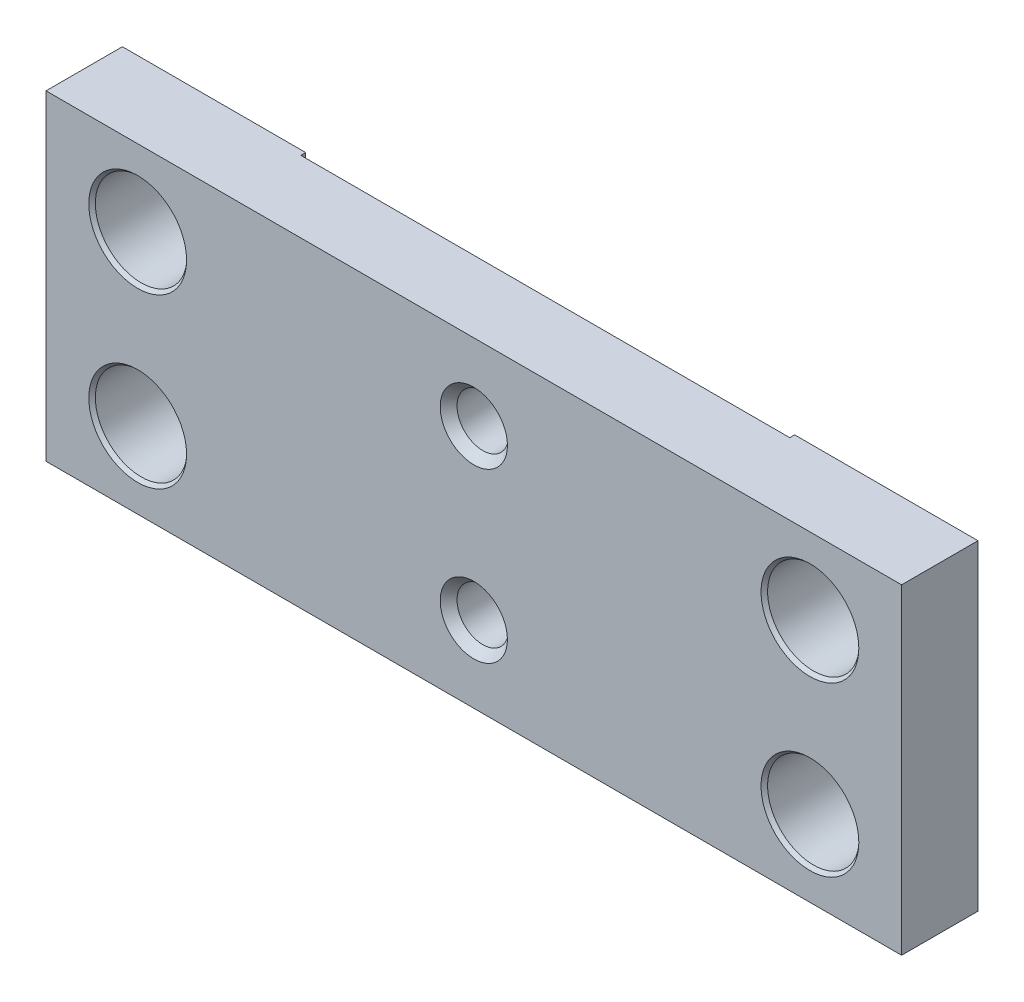
SolidWorks part; units mm, degrees
material "AISI 1018 Steel, Cold Rolled"
ref_plane "Front" through (0, 0, 0) normal (0, 0, 1) x (1, 0, 0)
ref_plane "Top" through (0, 0, 0) normal (0, 1, 0) x (1, 0, 0)
ref_plane "Right" through (0, 0, 0) normal (1, 0, 0) x (0, 0, -1)
sketch "Sketch1" plane through (0, 0, 0) normal (0, 0, 1) x (1, 0, 0)
  line L1 (-88.9, 0) -> (88.9, 0)
  line L2 (-88.9, 0) -> (-88.9, 66.675)
  line L3 (-88.9, 66.675) -> (88.9, 66.675)
  line L4 (88.9, 0) -> (88.9, 66.675)
  dimension "D1" = 66.675
  dimension "D2" = 177.8
extrude "Extrude1" add sketch "Sketch1" along normal blind 15.875
hole_wizard "1/2 Clearance Hole1" positions "Sketch12" profile "Sketch11" hole size "1/2" standard "Ansi Inch" end condition up to next
sketch "Sketch12" plane through (0, 0, 15.875) normal (0, 0, 1) x (1, 0, 0)
  line L0 (-69.85, 15.875) -> (69.85, 15.875) construction
  line L7 (-88.9, 33.3375) -> (88.9, 33.3375) construction
  line L8 (-88.9, 66.675) -> (-88.9, 0) construction
  line L9 (88.9, 0) -> (88.9, 66.675) construction
  line L12 (-69.85, 50.8) -> (69.85, 50.8) construction
  line L15 (0, 15.875) -> (0, 33.3375) construction
  line L16 (0, 33.3375) -> (0, 50.8) construction
  point P0 (-69.85, 50.8)
  point P1 (-69.85, 15.875)
  point P3 (69.85, 50.8)
  point P5 (69.85, 15.875)
  dimension "D1" = 34.925
  dimension "D3" = 139.7
sketch "Sketch11" plane through (-69.85, 50.8, 15.875) normal (1, 0, 0) x (0, -1, 0)
  line L0 (0, 0) -> (0, 15.875)
  line L1 (0, 15.875) -> (10.16, 15.875)
  line L2 (9.525, 15.1445) -> (9.525, 0.7305)
  line L3 (9.525, 0.7305) -> (10.16, 0)
  line L5 (10.16, 0) -> (0, 0)
  line L6 (-9.525, 0.7305) -> (-10.16, 0) construction
  line L7 (10.16, 15.875) -> (9.525, 15.1445)
  line L8 (-10.16, 15.875) -> (-9.525, 15.1445) construction
  line L11 (0, -6.35) -> (0, 107.95) construction
  dimension "Thru Hole Dia." = 19.05
  dimension "Thru Hole Depth" = 15.875
  dimension "Near C'Sink Dia." = 20.32
  dimension "Near C'Sink Angle" = 82
  dimension "Far C'Sink Dia." = 20.32
  dimension "Far C'Sink Angle" = 82
sketch "Sketch15" plane through (0, 0, 0) normal (0, 0, -1) x (-1, 0, 0)
  line L0 (-88.9, 66.675) -> (88.9, 66.675) construction
  line L1 (-50.8, 66.675) -> (50.8, 66.675)
  line L2 (-50.8, 66.675) -> (-50.8, 0)
  line L3 (-50.8, 0) -> (50.8, 0)
  line L4 (50.8, 66.675) -> (50.8, 0)
  line L5 (88.9, 0) -> (-88.9, 0) construction
  line L6 (88.9, 66.675) -> (88.9, 0) construction
  point P8 (0, 66.675)
  dimension "D1" = 38.1
extrude "Cut-Extrude1" cut sketch "Sketch15" against normal blind 1.016
sketch "Sketch17" plane through (0, 0, 0) normal (1, 0, 0) x (0, 0, -1)
  line L0 (-6.35, 0) -> (0, 10.9985)
  line L1 (-15.875, 0) -> (0, 0) construction
  line L2 (0, 0) -> (0, 66.675) construction
  line L3 (0, 10.9985) -> (0, 0)
  line L4 (0, 0) -> (-6.35, 0)
  line L5 (-15.875, 0) -> (-15.875, 66.675) construction
  dimension "D1" = 30
  dimension "D2" = 9.525
extrude "Cut-Extrude2" cut sketch "Sketch17" against normal mid plane 38.1
hole_wizard "1/2-13 Tapped Hole1" positions "Sketch14" profile "Sketch13" tap size "1/2-13" standard "Ansi Inch" end condition up to next
sketch "Sketch14" plane through (0, 0, 15.875) normal (0, 0, 1) x (1, 0, 0)
  line L0 (-69.85, 15.875) -> (69.85, 15.875) construction
  line L3 (-69.85, 50.8) -> (69.85, 50.8) construction
  point P0 (0, 50.8)
  point P1 (0, 15.875)
sketch "Sketch13" plane through (0, 50.8, 15.875) normal (1, 0, 0) x (0, -1, 0)
  line L0 (0, 0) -> (0, 14.859)
  line L1 (0, 14.859) -> (5.3581, 14.859)
  line L2 (5.3581, 14.859) -> (5.3581, 1.8715)
  line L3 (5.3581, 1.8715) -> (6.985, 0)
  line L5 (6.985, 0) -> (0, 0)
  line L6 (-5.3581, 1.8715) -> (-6.985, 0) construction
  line L11 (0, -6.35) -> (0, 107.95) construction
  dimension "Thru Tap Drill Dia." = 10.7163
  dimension "Thru Tap Drill Depth" = 14.859
  dimension "Near C'Sink Dia." = 13.97
  dimension "Near C'Sink Angle" = 82
cosmetic thread "Hole Thread3" parameters "D2"=12.7
cosmetic thread "Hole Thread4" parameters "D2"=12.7
sketch "Sketch18" [suppressed] plane through (0, 0, 0) normal (0, 0, -1) x (-1, 0, 0)
  circle A0 centre (-69.85, 50.8) radius 12.7
  dimension "D1" = 25.4
split line "Split Line1" [suppressed]
sketch "Sketch19" [suppressed] plane through (0, 0, 0) normal (0, 0, -1) x (-1, 0, 0)
  circle A0 centre (-69.85, 15.875) radius 12.7
  circle A1 centre (-69.85, 50.8) radius 12.7 construction
split line "Split Line2" [suppressed]
sketch "Sketch20" [suppressed] plane through (0, 0, 0) normal (0, 0, -1) x (-1, 0, 0)
  circle A0 centre (69.85, 50.8) radius 12.7
  circle A1 centre (-69.85, 50.8) radius 12.7 construction
split line "Split Line3" [suppressed]
sketch "Sketch21" [suppressed] plane through (0, 0, 0) normal (0, 0, -1) x (-1, 0, 0)
  circle A0 centre (69.85, 15.875) radius 12.7
  circle A1 centre (69.85, 50.8) radius 12.7 construction
split line "Split Line4" [suppressed]
sketch "Sketch22" [suppressed] plane through (0, 0, 15.875) normal (0, 0, 1) x (1, 0, 0)
  circle A0 centre (0, 50.8) radius 9.525
  dimension "D1" = 19.05
split line "Split Line5" [suppressed]
sketch "Sketch23" [suppressed] plane through (0, 0, 15.875) normal (0, 0, 1) x (1, 0, 0)
  circle A0 centre (0, 15.875) radius 9.525
  circle A1 centre (0, 50.8) radius 9.525 construction
split line "Split Line6" [suppressed]
